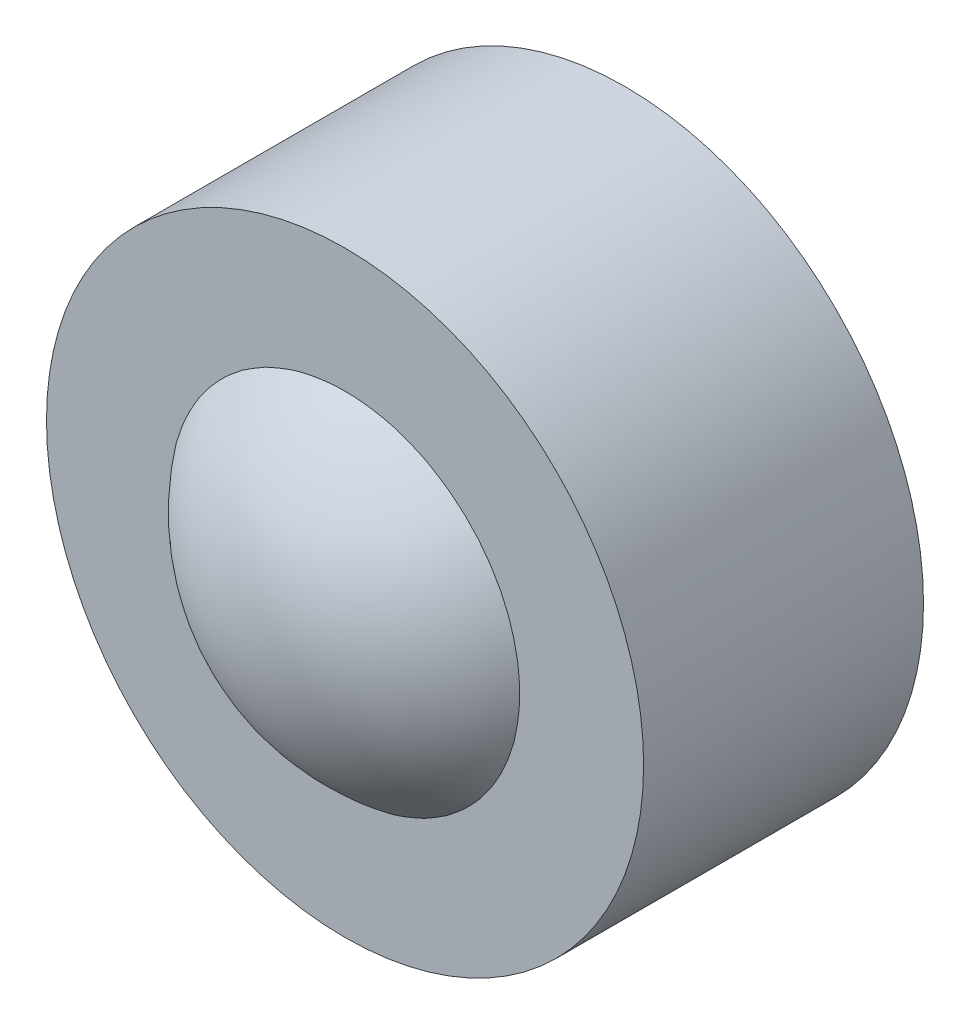
SolidWorks part; units mm, degrees
ref_plane "Ön Düzlem" through (0, 0, 0) normal (0, 0, 1) x (1, 0, 0)
ref_plane "Üst Düzlem" through (0, 0, 0) normal (0, 1, 0) x (1, 0, 0)
ref_plane "Sağ Düzlem" through (0, 0, 0) normal (1, 0, 0) x (0, 0, -1)
sketch "Sketch1" plane through (0, 0, 0) normal (0, 0, 1) x (1, 0, 0)
  circle A0 centre (0, 0) radius 4
  circle A1 centre (0, 0) radius 3 construction
  circle A2 centre (0, 0) radius 2
  dimension "D1" = 8
  dimension "D2" = 4
  dimension "D3" = 6
extrude "Boss-Extrude1" add sketch "Sketch1" along normal mid plane 3.75
sketch "Sketch2" plane through (0, 0, 0) normal (0, 0, 1) x (1, 0, 0)
  line L0 (0, -3) -> (0, 3.7954) construction
  line L1 (0, -3) -> (0, 3)
  circle A0 centre (0, 0) radius 3 construction
  arc A1 (0, 3) -> (0, -3) centre (0, 0) ccw
revolve "Revolve1" add sketch "Sketch2" angle 360 about L0
